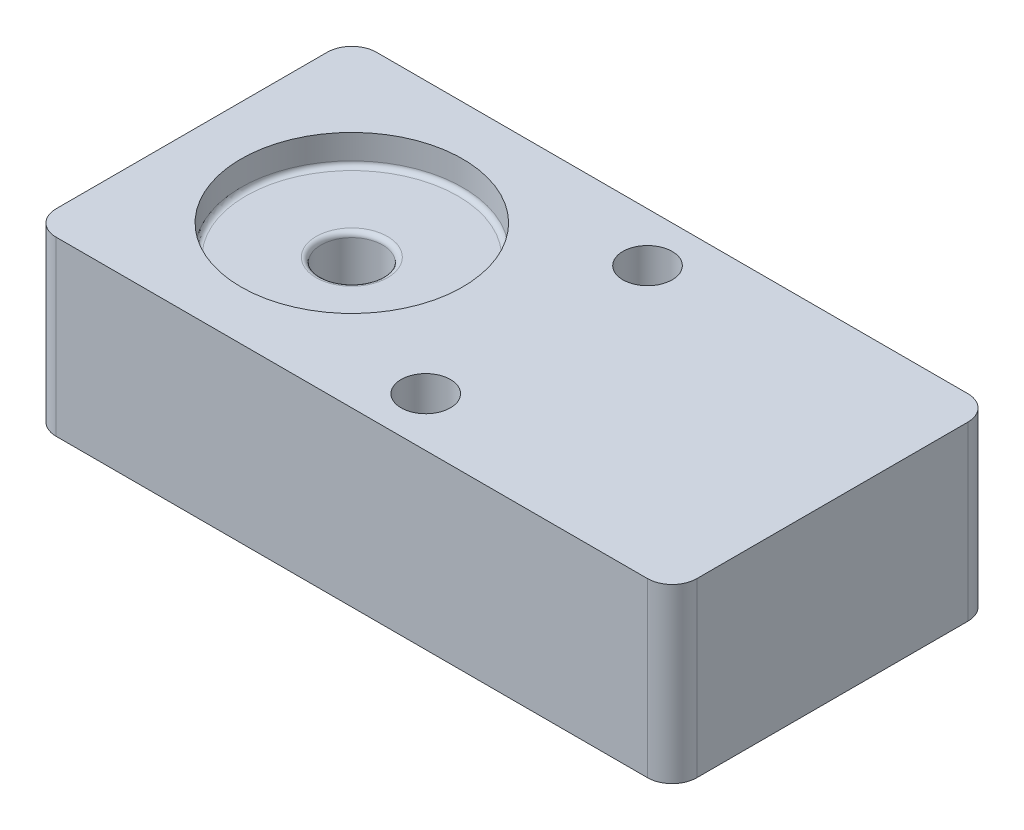
SolidWorks part; units mm, degrees
ref_plane "Plan de face" through (0, 0, 0) normal (0, 0, 1) x (1, 0, 0)
ref_plane "Plan de dessus" through (0, 0, 0) normal (0, 1, 0) x (1, 0, 0)
ref_plane "Plan de droite" through (0, 0, 0) normal (1, 0, 0) x (0, 0, -1)
sketch "Esquisse2" plane through (0, 0, 0) normal (0, 1, 0) x (1, 0, 0)
  line L1 (130, -65) -> (-130, -65)
  line L2 (130, -65) -> (130, 65)
  line L3 (130, 65) -> (-130, 65)
  line L4 (-130, -65) -> (-130, 65)
  line L5 (130, -65) -> (-130, 65) construction
  line L6 (130, 65) -> (-130, -65) construction
  point P0 (0, 0)
  dimension "D1" = 130
  dimension "D2" = 260
extrude "Boss.-Extru.2" add sketch "Esquisse2" along normal blind 70
sketch "Esquisse3" plane through (0, 70, 0) normal (0, 1, 0) x (1, 0, 0)
  line L0 (130, 65) -> (-130, 65) construction
  line L1 (-130, 65) -> (-130, -65) construction
  circle A0 centre (-65, 0) radius 45
  dimension "D1" = 65
  dimension "D2" = 90
  dimension "D3" = 65
extrude "Enlèv. mat.-Extru.1" cut sketch "Esquisse3" against normal blind 12
fillet "Congé1" radius 2 1 edges at (-65, 58, 45)
sketch "Esquisse4" plane through (0, 58, 0) normal (0, 1, 0) x (1, 0, 0)
  circle A0 centre (-65, 0) radius 12.5
extrude "Enlèv. mat.-Extru.2" cut sketch "Esquisse4" against normal blind 38
fillet "Congé2" radius 2 1 edges at (-65, 58, 12.5)
fillet "Congé3" radius 2 1 edges at (-65, 20, 12.5)
fillet "Congé4" radius 10 1 edges at (-130, 35, -65)
fillet "Congé5" radius 10 1 edges at (-130, 35, 65)
fillet "Congé6" radius 10 1 edges at (130, 35, 65)
fillet "Congé7" radius 10 1 edges at (130, 35, -65)
sketch "Esquisse6" plane through (0, 70, 0) normal (0, 1, 0) x (1, 0, 0)
  line L0 (-1000, 0) -> (49000, 0) construction
  line L1 (0, -1000) -> (0, 49000) construction
  line L2 (-1000, 45) -> (49000, 45) construction
  line L3 (10, -1000) -> (10, 49000) construction
  line L4 (120, 65) -> (-120, 65) construction
  circle A0 centre (10, 45) radius 10
  circle A1 centre (10, -45) radius 10
  dimension "D1" = 20
  dimension "D2" = 10
extrude "Enlèv. mat.-Extru.3" cut sketch "Esquisse6" against normal through all
